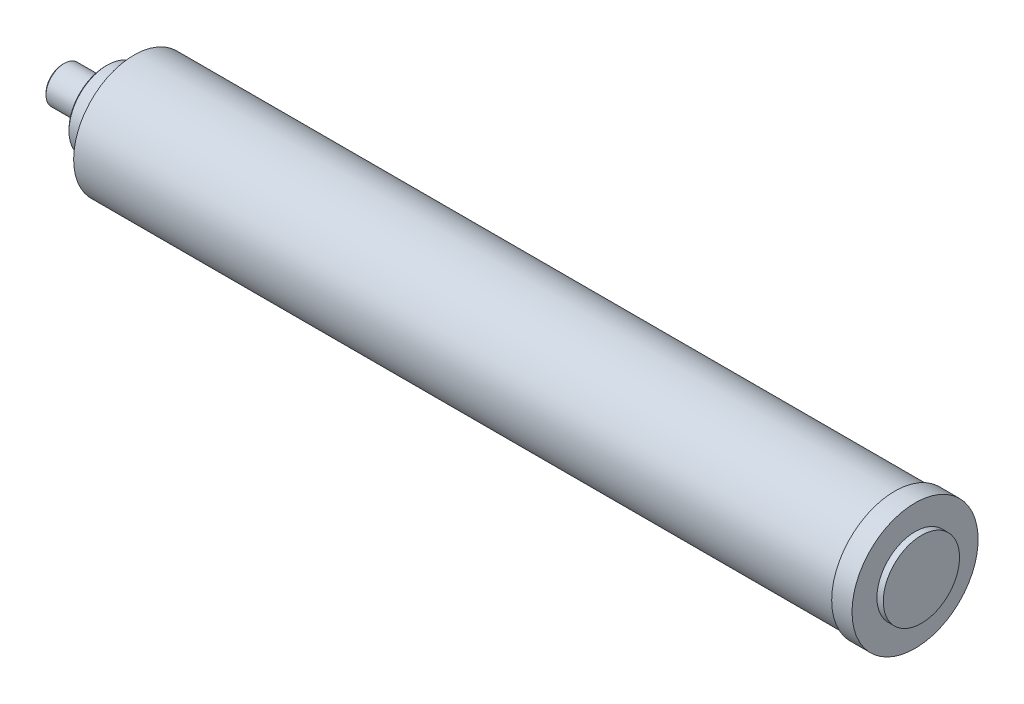
SolidWorks part; units mm, degrees
ref_plane "Plan de face" through (0, 0, 0) normal (0, 0, 1) x (1, 0, 0)
ref_plane "Plan de dessus" through (0, 0, 0) normal (0, 1, 0) x (1, 0, 0)
ref_plane "Plan de droite" through (0, 0, 0) normal (1, 0, 0) x (0, 0, -1)
sketch "Esquisse1" plane through (0, 0, 0) normal (0, 0, 1) x (1, 0, 0)
  line L0 (0, 0) -> (0, 11.395)
  line L1 (0, 11.395) -> (26.75, 11.395)
  line L2 (26.75, 11.395) -> (26.75, 23.8)
  line L3 (26.75, 23.8) -> (44.5, 23.8)
  line L4 (44.5, 23.8) -> (44.5, 37.65)
  line L5 (44.5, 37.65) -> (519.3, 37.65)
  line L6 (519.3, 37.65) -> (519.3, 39.35)
  line L7 (519.3, 39.35) -> (532, 39.35)
  line L8 (532, 39.35) -> (532, 23.8)
  line L9 (532, 23.8) -> (535.96, 23.8)
  line L10 (535.96, 23.8) -> (535.96, 0)
  line L11 (535.96, 0) -> (0, 0)
  line L12 (0, 0) -> (535.96, 0) construction
  point P3 (44.5, 30.725)
  point P14 (13.375, 11.395)
  dimension "D1" = 23.8
  dimension "D2" = 37.65
  dimension "D3" = 39.35
  dimension "D4" = 23.8
  dimension "D5" = 487.5
  dimension "D6" = 44.5
  dimension "D7" = 12.7
  dimension "D8" = 11.395
  dimension "D9" = 3.96
  dimension "D10" = 26.75
revolve "Révolution1" add sketch "Esquisse1" angle 360 about L12
chamfer "Chanfrein1" distance 1 angle 45 2 edges at (26.75, 0, 23.8) (0, 0, 11.395)
